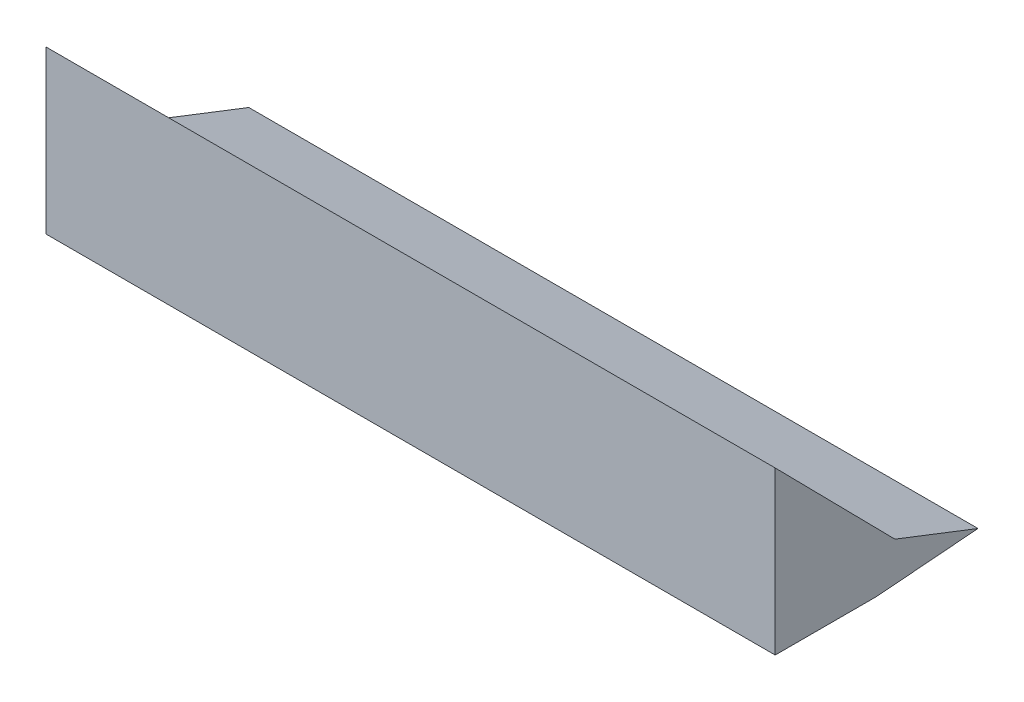
SolidWorks part; units mm, degrees
ref_plane "Front Plane" through (0, 0, 0) normal (0, 0, 1) x (1, 0, 0)
ref_plane "Top Plane" through (0, 0, 0) normal (0, 1, 0) x (1, 0, 0)
ref_plane "Right Plane" through (0, 0, 0) normal (1, 0, 0) x (0, 0, -1)
sketch "Sketch1" plane through (0, 0, 0) normal (1, 0, 0) x (0, 0, -1)
  line L2 (0, 0) -> (0, 40)
  line L3 (50.0601, 2.0276) -> (29.5554, 10)
  line L4 (29.5554, 10) -> (0, 40)
  line L6 (0, 0) -> (25, 0)
  line L7 (25, 0) -> (50.0601, 2.0276)
  dimension "D1" = 184.626
  dimension "40" = 40
  dimension "D2" = 30
  dimension "D3" = 22
  dimension "D4" = 25
  dimension "D5" = 50.0601
extrude "Boss-Extrude1" add sketch "Sketch1" along normal blind 180
